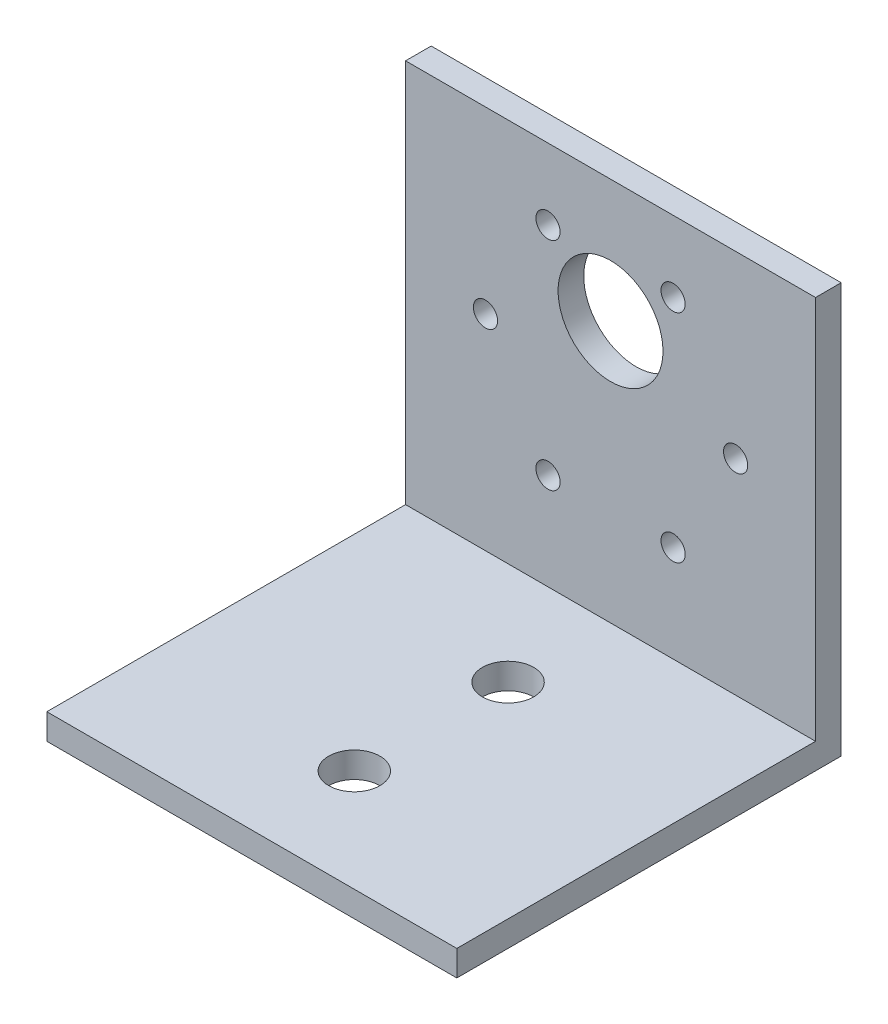
SolidWorks part; units mm, degrees
ref_plane "Front Plane" through (0, 0, 0) normal (0, 0, 1) x (1, 0, 0)
ref_plane "Top Plane" through (0, 0, 0) normal (0, 1, 0) x (1, 0, 0)
ref_plane "Right Plane" through (0, 0, 0) normal (1, 0, 0) x (0, 0, -1)
sketch "Sketch1" plane through (0, 0, 0) normal (0, 0, 1) x (1, 0, 0)
  line L0 (25.4, 50.8) -> (25.4, 0) construction
  line L1 (0, 0) -> (50.8, 0)
  line L2 (0, 0) -> (0, 50.8)
  line L3 (0, 50.8) -> (50.8, 50.8)
  line L4 (50.8, 0) -> (50.8, 50.8)
  line L6 (25.4, 28.575) -> (57.4013, 84.0029) construction
  line L7 (25.4, 28.575) -> (62.6916, -36.0159) construction
  circle A0 centre (25.4, 35.575) radius 6.5
  circle A1 centre (25.4, 28.575) radius 18.5 construction
  circle A2 centre (9.9, 28.575) radius 1.5
  circle A3 centre (40.9, 28.575) radius 1.5
  circle A4 centre (33.15, 15.1516) radius 1.5
  circle A5 centre (17.65, 15.1516) radius 1.5
  circle A6 centre (17.65, 41.9984) radius 1.5
  circle A7 centre (33.15, 41.9984) radius 1.5
  circle A8 centre (25.4, 28.575) radius 15.5 construction
  point P1 (0, 0)
  point P2 (0, 0)
  dimension "D3" = 13
  dimension "D4" = 37
  dimension "D7" = 3
  dimension "D8" = 31
  dimension "D1" = 50.8
  dimension "D2" = 50.8
  dimension "D5" = 7
  dimension "D6" = 22.225
extrude "Boss-Extrude1" add sketch "Sketch1" along normal blind 3.175
sketch "Sketch2" plane through (0, 0, 3.175) normal (0, 0, 1) x (1, 0, 0)
  line L0 (50.8, 0) -> (50.8, 50.8) construction
  line L1 (0, 0) -> (50.8, 0)
  line L2 (0, 0) -> (0, 3.175)
  line L3 (0, 3.175) -> (50.8, 3.175)
  line L4 (50.8, 0) -> (50.8, 3.175)
  dimension "D1" = 3.175
extrude "Boss-Extrude2" add sketch "Sketch2" along normal blind 44.45
sketch "Sketch3" plane through (0, 3.175, 0) normal (0, 1, 0) x (1, 0, 0)
  line L0 (25.4, -47.625) -> (25.4, -3.175) construction
  line L1 (50.8, -47.625) -> (0, -47.625) construction
  line L2 (50.8, -3.175) -> (0, -3.175) construction
  circle A0 centre (25.4, -15.875) radius 3.175
  circle A1 centre (25.4, -34.925) radius 3.175
  point P12 (26.6653, -36.5582)
  dimension "D1" = 6.35
  dimension "D2" = 6.35
  dimension "D3" = 19.05
  dimension "D4" = 12.7
extrude "Cut-Extrude1" cut sketch "Sketch3" against normal through all
